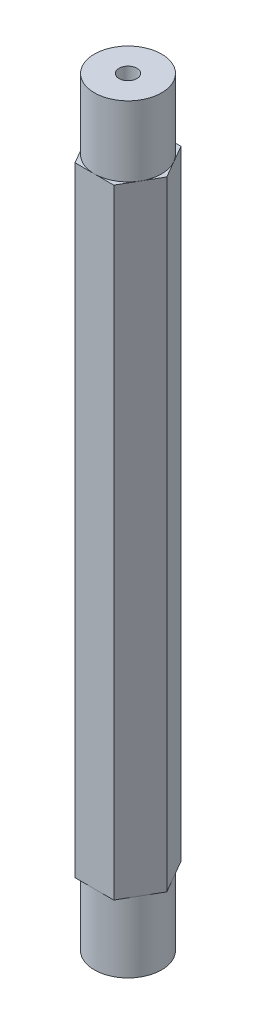
SolidWorks part; units mm, degrees
material "Alum Plate"
ref_plane "Front Plane" through (0, 0, 0) normal (0, 0, 1) x (1, 0, 0)
ref_plane "Top Plane" through (0, 0, 0) normal (0, 1, 0) x (1, 0, 0)
ref_plane "Right Plane" through (0, 0, 0) normal (1, 0, 0) x (0, 0, -1)
other "Bounding Box"
ref_plane "Default Plane" through (-8.9266, -12.7485, 0) normal (-0.1736, 0.9848, 0) x (0.9848, 0.1736, 0)
sketch "Sketch1" plane through (0, 0, 0) normal (0, 1, 0) x (1, 0, 0)
  line L1 (1.3748, -2.3812) -> (2.7496, 0)
  line L2 (2.7496, 0) -> (1.3748, 2.3813)
  line L3 (1.3748, 2.3813) -> (-1.3748, 2.3813)
  line L4 (-1.3748, 2.3813) -> (-2.7496, 0)
  line L5 (-2.7496, 0) -> (-1.3748, -2.3812)
  line L6 (-1.3748, -2.3812) -> (1.3748, -2.3812)
  circle A0 centre (0, 0) radius 2.3813 construction
  circle A1 centre (0, 0) radius 0.635
  dimension "D2" = 1.27
  dimension "D1" = 4.7625
extrude "Boss-Extrude1" add sketch "Sketch1" along normal mid plane 43.8912
sketch "Sketch2" plane through (0, 21.9456, 0) normal (0, 1, 0) x (1, 0, 0)
  circle A0 centre (0, 0) radius 2.3813
  circle A1 centre (0, 0) radius 0.635 construction
  circle A2 centre (0, 0) radius 0.635
  dimension "D1" = 4.7625
extrude "Boss-Extrude2" add sketch "Sketch2" along normal blind 4.9784
sketch "Sketch3" plane through (0, -21.9456, 0) normal (0, -1, 0) x (1, 0, 0)
  circle A0 centre (0, 0) radius 0.635 construction
  circle A1 centre (0, 0) radius 0.635
  circle A2 centre (0, 0) radius 2.3813
  dimension "D1" = 4.7625
extrude "Boss-Extrude3" add sketch "Sketch3" along normal blind 4.9784
